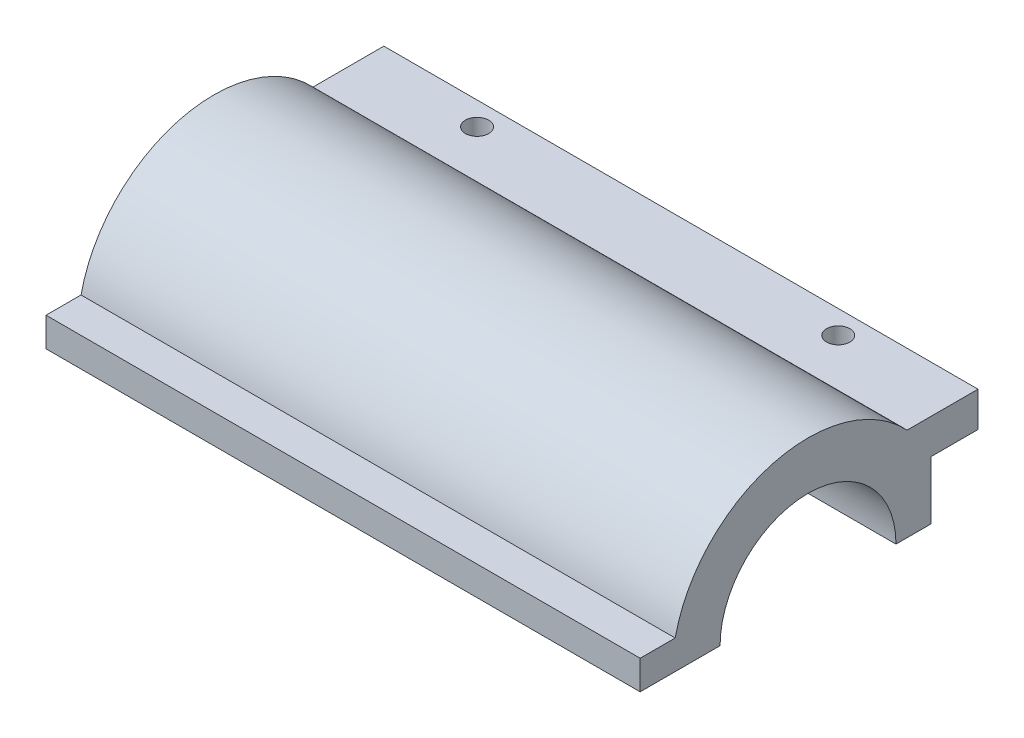
SolidWorks part; units mm, degrees
ref_plane "Front Plane" through (0, 0, 0) normal (0, 0, 1) x (1, 0, 0)
ref_plane "Top Plane" through (0, 0, 0) normal (0, 1, 0) x (1, 0, 0)
ref_plane "Right Plane" through (0, 0, 0) normal (1, 0, 0) x (0, 0, -1)
sketch "Sketch1" plane through (0, 0, 0) normal (1, 0, 0) x (0, 0, -1)
  line L0 (12.1579, -12.3507) -> (15.1579, -12.3507)
  line L2 (-9.8021, -9.8507) -> (-9.8021, -12.3507)
  line L3 (-9.8021, -12.3507) -> (-2.9421, -12.3507)
  line L4 (19.1979, -4.3507) -> (19.1979, -7.3507)
  line L5 (15.1579, -12.3507) -> (15.1579, -7.3507)
  line L6 (15.1579, -7.3507) -> (19.1979, -7.3507)
  line L7 (-9.8021, -9.8507) -> (-6.7962, -9.8507)
  line L8 (19.1979, -4.3507) -> (13.111, -4.3507)
  arc A0 (12.1579, -12.3507) -> (-2.9421, -12.3507) centre (4.6079, -12.3507) ccw
  arc A1 (13.111, -4.3507) -> (-6.7962, -9.8507) centre (4.6079, -12.3507) ccw
  dimension "D3" = 15.1
  dimension "D1" = 2.5
  dimension "D2" = 3
  dimension "D4" = 14.41
  dimension "D5" = 3
  dimension "D6" = 5
extrude "Boss-Extrude1" add sketch "Sketch1" along normal blind 51
sketch "Sketch2" plane through (0, -4.3507, 0) normal (0, 1, 0) x (1, 0, 0)
  line L0 (51, 19.1979) -> (0, 19.1979) construction
  line L1 (0, 19.1979) -> (0, 13.111) construction
  line L2 (51, 19.1979) -> (51, 13.111) construction
  circle A0 centre (10, 17.1979) radius 1
  circle A1 centre (41, 17.1979) radius 1
  dimension "D1" = 2
  dimension "D2" = 10
  dimension "D3" = 10
extrude "Cut-Extrude1" cut sketch "Sketch2" against normal blind 789
